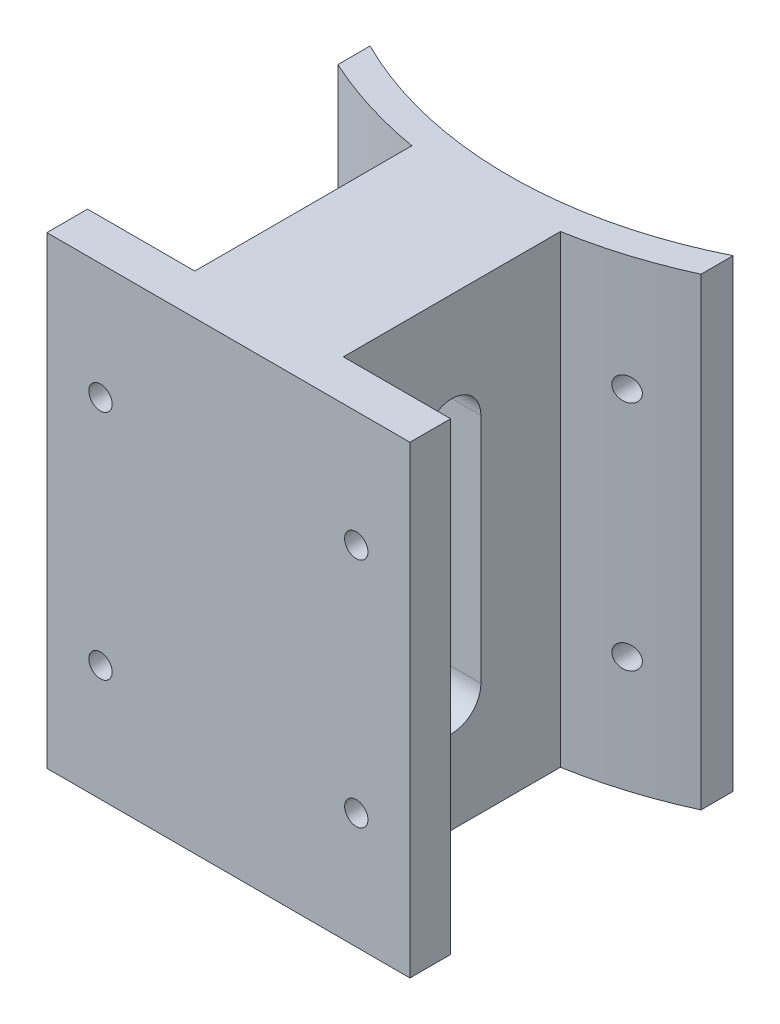
SolidWorks part; units mm, degrees
ref_plane "Front Plane" through (0, 0, 0) normal (0, 0, 1) x (1, 0, 0)
ref_plane "Top Plane" through (0, 0, 0) normal (0, 1, 0) x (1, 0, 0)
ref_plane "Right Plane" through (0, 0, 0) normal (1, 0, 0) x (0, 0, -1)
sketch "Sketch1" plane through (0, 0, 0) normal (0, 1, 0) x (1, 0, 0)
  line L0 (0, 0) -> (0, -88.9) construction
  line L1 (-16.2666, -141.3784) -> (-39.7573, -141.3784)
  line L3 (39.7573, -86.5559) -> (39.7573, -79.5146)
  line L5 (-39.7573, -86.5559) -> (-39.7573, -79.5146)
  line L6 (24.7975, -141.3784) -> (-39.7573, -79.5146) construction
  line L7 (39.7573, -79.5146) -> (-16.2666, -133.2031) construction
  line L9 (16.2666, -141.3784) -> (16.2666, -93.8507)
  line L11 (-16.2666, -141.3784) -> (-16.2666, -93.8507)
  line L12 (16.2666, -141.3784) -> (-16.2666, -93.8507) construction
  line L13 (16.2666, -93.8507) -> (-16.2666, -141.3784) construction
  line L14 (39.7573, -150.2877) -> (-39.7573, -150.2877)
  line L15 (39.7573, -150.2877) -> (39.7573, -141.3784)
  line L16 (39.7573, -141.3784) -> (16.2666, -141.3784)
  line L17 (-39.7573, -150.2877) -> (-39.7573, -141.3784)
  arc A0 (-39.7573, -79.5146) -> (39.7573, -79.5146) centre (0, 0) ccw
  arc A1 (-39.7573, -86.5559) -> (-16.2666, -93.8507) centre (0, 0) ccw
  circle A2 centre (0, 0) radius 95.25 construction
  circle A3 centre (0, 0) radius 88.9 construction
  arc A4 (16.2666, -93.8507) -> (39.7573, -86.5559) centre (0, 0) ccw
  point P3 (0, -117.6146)
  point P4 (0, -117.6146)
  point P18 (0, -155.7146)
  dimension "D1" = 177.8
  dimension "D3" = 6.35
extrude "Boss-Extrude1" add sketch "Sketch1" along normal blind 101.6
sketch "Sketch2" plane through (16.2666, 0, 0) normal (1, 0, 0) x (0, 0, -1)
  line L0 (-117.6146, 101.6) -> (-117.6146, 0) construction
  line L1 (-141.3784, 101.6) -> (-93.8507, 101.6) construction
  line L2 (-141.3784, 0) -> (-93.8507, 0) construction
  line L3 (-117.6146, 75.4343) -> (-117.6146, 24.6343) construction
  line L4 (-111.2646, 75.4343) -> (-111.2646, 24.6343)
  line L5 (-123.9646, 75.4343) -> (-123.9646, 24.6343)
  arc A0 (-111.2646, 75.4343) -> (-123.9646, 75.4343) centre (-117.6146, 75.4343) ccw
  arc A1 (-123.9646, 24.6343) -> (-111.2646, 24.6343) centre (-117.6146, 24.6343) ccw
  point P8 (-117.6146, 50.0343)
  dimension "D2" = 6.35
  dimension "D1" = 25.4
extrude "Cut-Extrude1" cut sketch "Sketch2" against normal through all
hole_wizard "Tap Drill for 1/4-20 Tap2" positions "Sketch3" profile "Sketch4" hole size "1/4-20" standard "ANSI Inch" end condition through all
sketch "Sketch3" plane through (0, 0, 150.2877) normal (0, 0, 1) x (1, 0, 0)
  line L0 (-16.2666, 101.6) -> (-39.7573, 101.6) construction
  line L1 (-16.2666, 101.6) -> (-39.7573, 101.6) construction
  line L2 (0, 101.6) -> (0, 0) construction
  line L3 (-39.7573, 101.6) -> (39.7573, 101.6) construction
  line L4 (-39.7573, 0) -> (39.7573, 0) construction
  line L6 (-28.0119, 101.6) -> (-28.0119, 0) construction
  line L8 (-39.7573, 50.8) -> (39.7573, 50.8) construction
  line L9 (-39.7573, 101.6) -> (-39.7573, 0) construction
  line L10 (39.7573, 101.6) -> (39.7573, 0) construction
  point P24 (-28.0119, 76.2)
  point P27 (-28.0119, 25.4)
  point P28 (28.0119, 25.4)
  point P29 (28.0119, 76.2)
  dimension "D1" = 50.8
sketch "Sketch4" plane through (28.0119, 76.2, 150.2877) normal (1, 0, 0) x (0, -1, 0)
  line L0 (0, 0) -> (0, 70.7731)
  line L1 (0, 70.7731) -> (2.5527, 70.7731)
  line L2 (2.5527, 70.7731) -> (2.5527, 0)
  line L5 (2.5527, 0) -> (0, 0)
  line L11 (0, -6.35) -> (0, 107.95) construction
  dimension "Thru Hole Dia." = 5.1054
  dimension "Thru Hole Depth" = 70.7731
